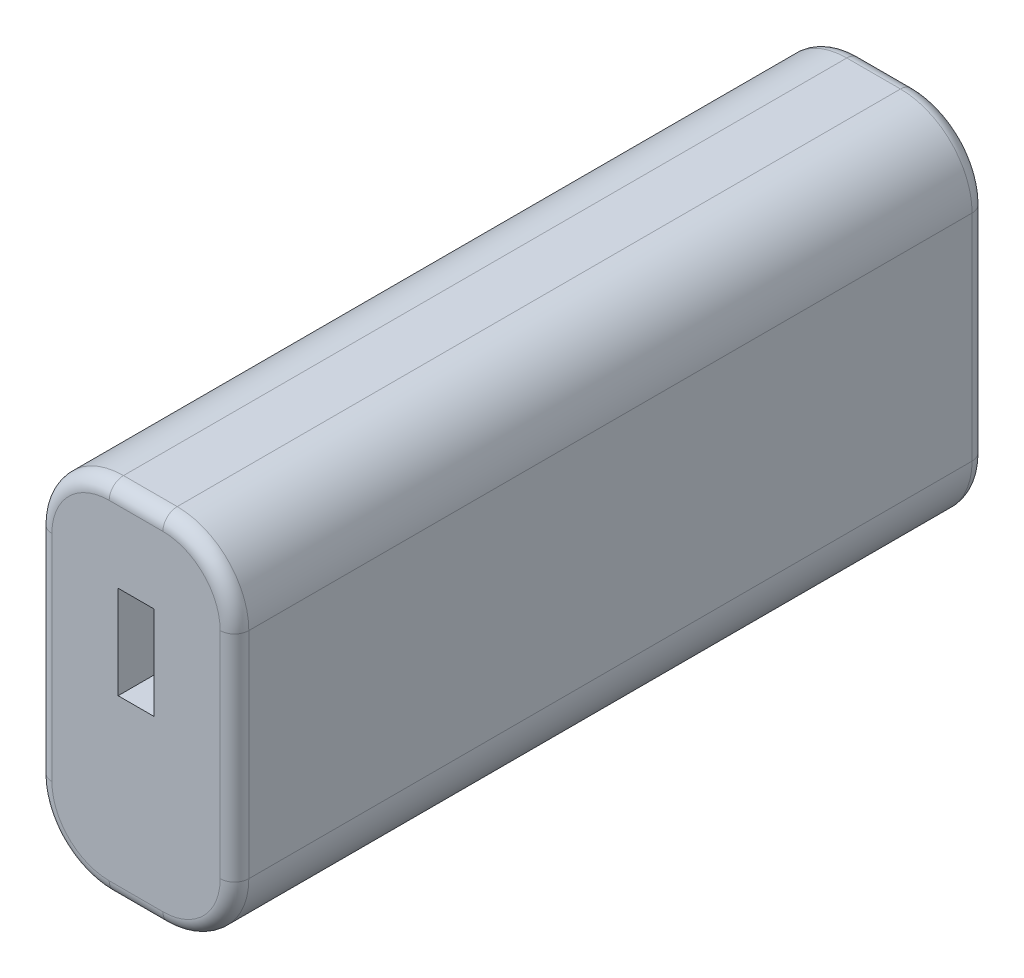
SolidWorks part; units mm, degrees
ref_plane "Front Plane" through (0, 0, 0) normal (0, 0, 1) x (1, 0, 0)
ref_plane "Top Plane" through (0, 0, 0) normal (0, 1, 0) x (1, 0, 0)
ref_plane "Right Plane" through (0, 0, 0) normal (1, 0, 0) x (0, 0, -1)
sketch "Sketch1" plane through (0, 0, 0) normal (0, 0, 1) x (1, 0, 0)
  line L0 (0, 10) -> (0, 40)
  line L1 (10, 50) -> (17.5, 50)
  line L2 (27.5, 40) -> (27.5, 10)
  line L3 (17.5, 0) -> (10, 0)
  arc A0 (27.5, 10) -> (17.5, 0) centre (17.5, 10) cw
  arc A1 (17.5, 50) -> (27.5, 40) centre (17.5, 40) cw
  arc A2 (0, 40) -> (10, 50) centre (10, 40) cw
  arc A3 (0, 10) -> (10, 0) centre (10, 10) ccw
  point P13 (0, 0)
  dimension "D1" = 10
extrude "Boss-Extrude1" add sketch "Sketch1" along normal blind 105
fillet "Fillet1" radius 2 16 edges at (24.5711, 2.9289, 0) (13.75, 0, 0) (2.9289, 2.9289, 0) (0, 25, 0) (2.9289, 47.0711, 0) (13.75, 50, 0) (24.5711, 47.0711, 0) (27.5, 25, 105) (24.5711, 2.9289, 105) (13.75, 0, 105) (2.9289, 2.9289, 105) (0, 25, 105) (2.9289, 47.0711, 105) (13.75, 50, 105) (27.5, 25, 0) (24.5711, 47.0711, 105)
sketch "Sketch2" plane through (0, 0, 105) normal (0, 0, 1) x (1, 0, 0)
  line L0 (25.5, 25) -> (2, 25) construction
  line L1 (25.5, 10) -> (25.5, 40) construction
  line L2 (2, 40) -> (2, 10) construction
  line L4 (13.75, 38) -> (11.25, 38)
  line L5 (13.75, 38) -> (16.25, 38)
  line L6 (16.25, 38) -> (16.25, 25)
  line L7 (16.25, 25) -> (11.25, 25)
  line L8 (11.25, 25) -> (11.25, 38)
extrude "Cut-Extrude1" cut sketch "Sketch2" against normal blind 20
